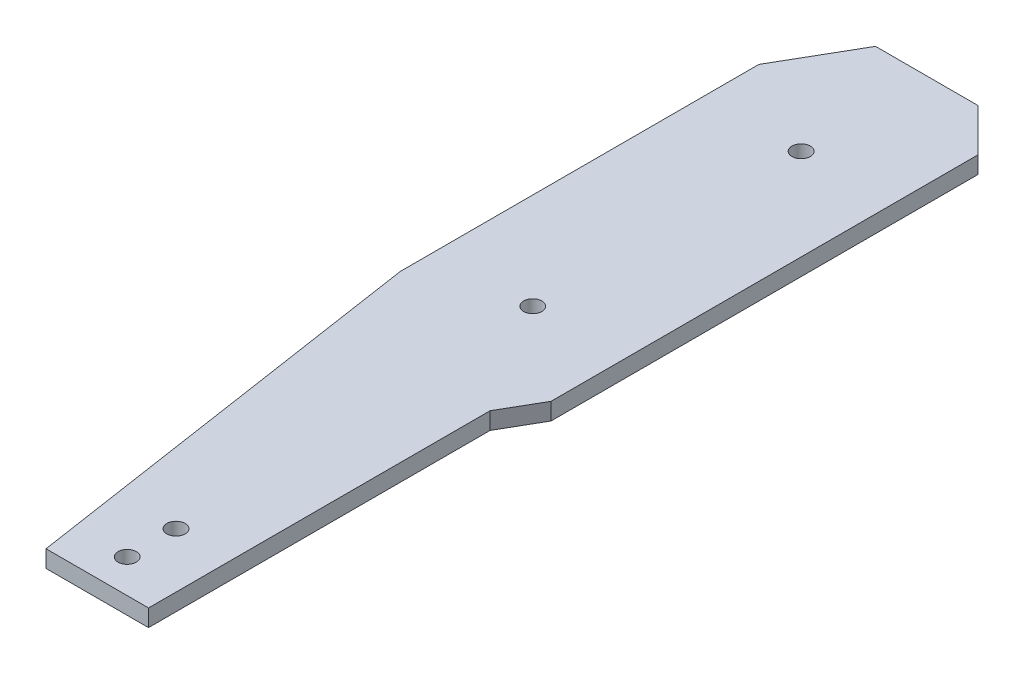
SolidWorks part; units mm, degrees
ref_plane "Front Plane" through (0, 0, 0) normal (0, 0, 1) x (1, 0, 0)
ref_plane "Top Plane" through (0, 0, 0) normal (0, 1, 0) x (1, 0, 0)
ref_plane "Right Plane" through (0, 0, 0) normal (1, 0, 0) x (0, 0, -1)
sketch "Sketch1" plane through (0, 0, 0) normal (0, 1, 0) x (1, 0, 0)
  line L0 (1.719, 61.2346) -> (-10.281, 61.2346)
  line L1 (-10.281, 61.2346) -> (-15.281, 52.5743)
  line L2 (-15.281, 52.5743) -> (-15.281, 10.5743)
  line L6 (4.1056, -38.2921) -> (4.1056, 1.7079)
  line L7 (4.1056, 1.7079) -> (6.719, 6.2346)
  line L8 (6.719, 6.2346) -> (6.719, 56.2346)
  line L9 (6.719, 56.2346) -> (1.719, 61.2346)
  line L10 (-15.281, 10.5743) -> (-7.9017, -38.2921)
  line L11 (-7.9017, -38.2921) -> (4.1056, -38.2921)
  point P2 (0, 0)
  dimension "D1" = 12
  dimension "D2" = 22
  dimension "D3" = 120
  dimension "D4" = 135
  dimension "D5" = 42
  dimension "D6" = 50
  dimension "D7" = 40
  dimension "D8" = 10
extrude "Boss-Extrude1" add sketch "Sketch1" along normal blind 2
scale "Scale1" scale about centroid uniform scaling yes scale factor 1.4
sketch "Sketch2" plane through (0, 2.4, 0) normal (0, 1, 0) x (1, 0, 0)
  line L0 (-41.7535, 76.514) -> (35.1413, 76.514) construction
  line L1 (4.0006, 79.514) -> (-12.7994, 79.514) construction
  line L2 (11.0006, 2.514) -> (11.0006, 72.514) construction
  line L3 (-13.4994, 76.514) -> (5.5006, 76.514) construction
  line L4 (-13.4994, 76.514) -> (-13.4994, -3.486) construction
  line L5 (-13.4994, -3.486) -> (5.5006, -3.486) construction
  line L6 (5.5006, 76.514) -> (5.5006, -3.486) construction
  line L7 (-41.7535, 36.514) -> (35.1413, 36.514) construction
  circle A0 centre (-3.9994, 14.514) radius 1.5
  circle A1 centre (-3.9994, 58.514) radius 1.5
  point P16 (0, 0)
  dimension "D6" = 3
  dimension "D1" = 3
  dimension "D2" = 80
  dimension "D3" = 19
  dimension "D4" = 5.5
  dimension "D5" = 40
  dimension "D7" = 9.5
  dimension "D8" = 22
  dimension "D9" = 22
extrude "Cut-Extrude1" cut sketch "Sketch2" against normal through all
sketch "Sketch3" plane through (0, 2.4, 0) normal (0, 1, 0) x (1, 0, 0)
  line L0 (-1.6582, -66.8692) -> (-1.6582, -32.6921) construction
  line L1 (7.3418, -59.8234) -> (-11.6582, -59.8234) construction
  line L2 (7.3418, -59.8234) -> (7.3418, -40.8234) construction
  line L3 (7.3418, -40.8234) -> (-11.6582, -40.8234) construction
  line L4 (-11.6582, -59.8234) -> (-11.6582, -40.8234) construction
  circle A0 centre (-1.6582, -46.3234) radius 1.5
  circle A1 centre (-1.6582, -54.3234) radius 1.5
  dimension "D4" = 3
  dimension "D1" = 19
  dimension "D2" = 19
  dimension "D3" = 9
  dimension "D5" = 5.5
  dimension "D6" = 5.5
extrude "Cut-Extrude2" cut sketch "Sketch3" against normal through all
